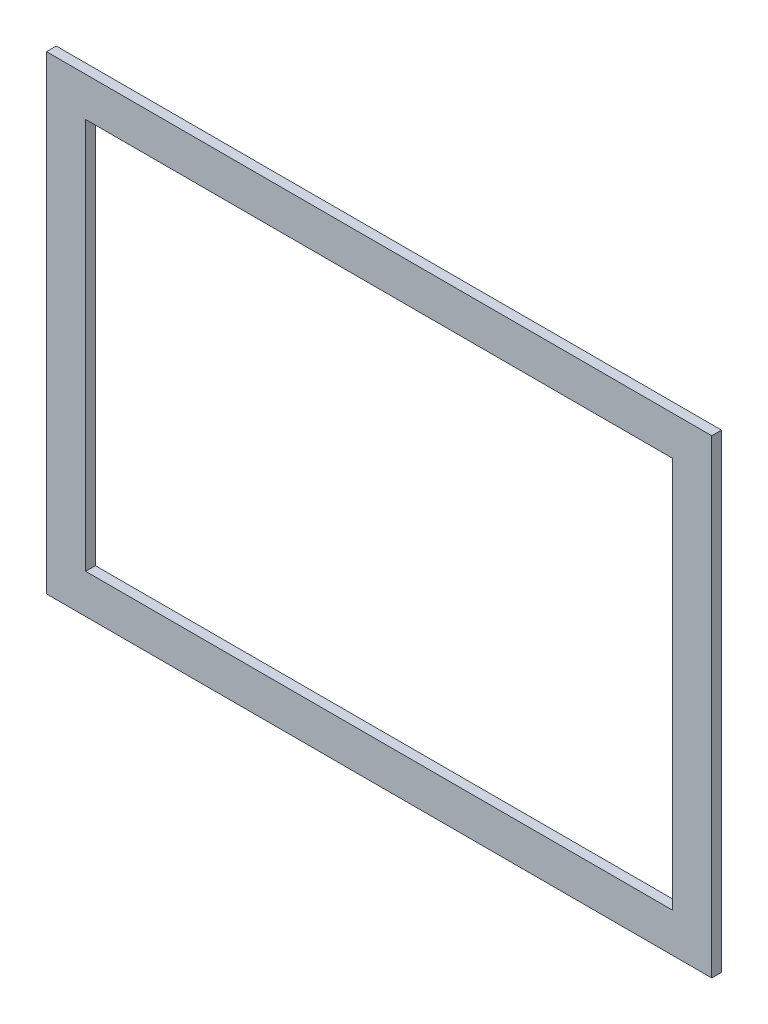
SolidWorks part; units mm, degrees
ref_plane "Plan de face" through (0, 0, 0) normal (0, 0, 1) x (1, 0, 0)
ref_plane "Plan de dessus" through (0, 0, 0) normal (0, 1, 0) x (1, 0, 0)
ref_plane "Plan de droite" through (0, 0, 0) normal (1, 0, 0) x (0, 0, -1)
sketch "Esquisse1" plane through (0, 0, 0) normal (0, 0, 1) x (1, 0, 0)
  line L1 (0, 0) -> (-680, 0)
  line L2 (0, 0) -> (0, 480)
  line L3 (0, 480) -> (-680, 480)
  line L4 (-680, 0) -> (-680, 480)
  line L5 (-640, 440) -> (-40, 440)
  line L6 (-640, 440) -> (-640, 40)
  line L7 (-640, 40) -> (-40, 40)
  line L8 (-40, 440) -> (-40, 40)
  dimension "D1" = 680
  dimension "D2" = 480
  dimension "D3" = 40
  dimension "D4" = 40
  dimension "D5" = 40
  dimension "D6" = 40
extrude "Boss.-Extru.1" add sketch "Esquisse1" along normal blind 10
